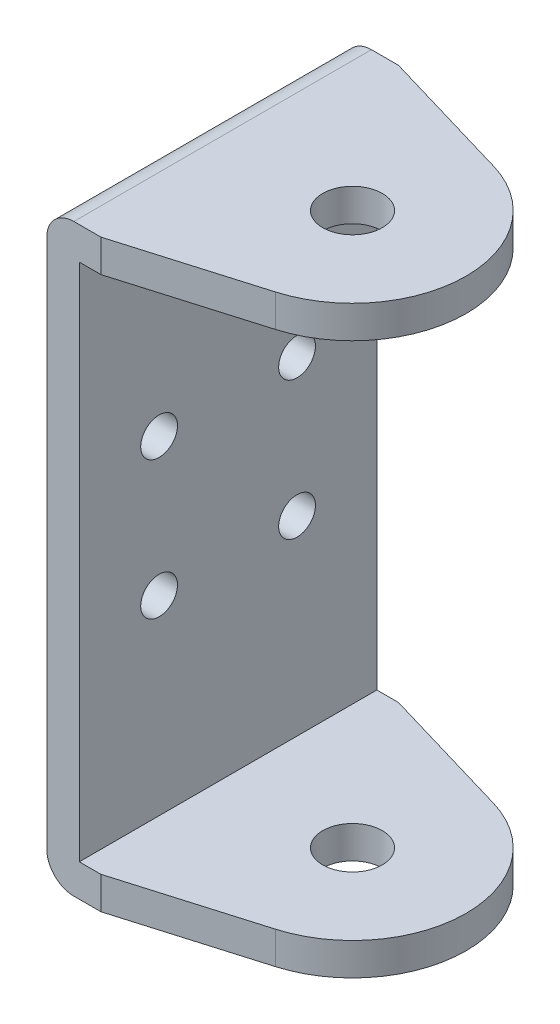
SolidWorks part; units mm, degrees
ref_plane "前基準面" through (0, 0, 0) normal (0, 0, 1) x (1, 0, 0)
ref_plane "上基準面" through (0, 0, 0) normal (0, 1, 0) x (1, 0, 0)
ref_plane "右基準面" through (0, 0, 0) normal (1, 0, 0) x (0, 0, -1)
sketch "草圖1" plane through (0, 0, 0) normal (0, 0, 1) x (1, 0, 0)
  line L0 (0, -54) -> (-45, -54)
  line L1 (0, 48) -> (-44, 48)
  line L2 (44, -48) -> (-44, -48) construction
  line L3 (0, -48) -> (-44, -48)
  line L4 (-44, 48) -> (-44, -48)
  line L5 (0, 0) -> (-44, -48) construction
  line L6 (0, 0) -> (-44, 48) construction
  line L7 (-50, 49) -> (-50, -49)
  line L8 (0, 54) -> (-45, 54)
  line L9 (50, -54) -> (-50, -54) construction
  line L10 (0, 65.9432) -> (0, -89.7922) construction
  line L11 (0, 54) -> (0, 48)
  line L12 (0, -48) -> (0, -54)
  line L13 (50, 54) -> (-50, 54) construction
  line L14 (44, 48) -> (-44, 48) construction
  line L15 (50, 54) -> (50, -54) construction
  line L16 (44, 48) -> (44, -48) construction
  line L17 (-50, 54) -> (-50, -54) construction
  line L18 (-44, 48) -> (-44, -48) construction
  line L19 (0, 0) -> (-107.849, 0) construction
  arc A0 (-45, -54) -> (-50, -49) centre (-45, -49) cw
  arc A2 (-50, 49) -> (-45, 54) centre (-45, 49) cw
  point P0 (0, 0)
  dimension "D5" = 5
  dimension "D6" = 5
  dimension "D1" = 6
  dimension "D2" = 108
  dimension "D3" = 50
  dimension "D4" = 96
extrude "填料-伸長1" add sketch "草圖1" along normal mid plane 55
hole_wizard "M10 螺紋孔1" positions "草圖4" profile "草圖3" tap size "M10" standard "ISO" end condition through all
sketch "草圖4" plane through (0, 54, 0) normal (0, 1, 0) x (1, 0, 0)
  line L0 (0, 0) -> (-21, 0) construction
  point P4 (-21, 0)
  dimension "D1" = 21
sketch "草圖3" plane through (-21, 54, 0) normal (1, 0, 0) x (0, 0, 1)
  line L0 (0, 0) -> (0, 108)
  line L1 (0, 108) -> (4.25, 108)
  line L2 (4.25, 108) -> (4.25, 0)
  line L5 (4.25, 0) -> (0, 0)
  line L11 (0, -6.35) -> (0, 107.95) construction
  dimension "貫穿螺孔鑽直徑" = 8.5
  dimension "貫穿螺孔鑽深度" = 108
cosmetic thread "鑽孔螺紋1" parameters "D2"=10
sketch "草圖6" plane through (-50, 0, 0) normal (-1, 0, 0) x (0, 0, 1)
  line L1 (12.75, 12.75) -> (12.75, -12.75) construction
  line L2 (12.75, 0) -> (0, 0) construction
  line L3 (0, 0) -> (-12.75, 0) construction
  line L4 (-12.75, -12.75) -> (-12.75, 12.75) construction
  circle A0 centre (12.75, 12.75) radius 3.4
  circle A1 centre (-12.75, 12.75) radius 3.4
  circle A2 centre (-12.75, -12.75) radius 3.4
  circle A3 centre (12.75, -12.75) radius 3.4
  dimension "D3" = 6.8
  dimension "D4" = 6.8
  dimension "D1" = 25.5
  dimension "D2" = 25.5
extrude "除料-伸長1" cut sketch "草圖6" against normal blind 10
cosmetic thread "裝飾螺紋線2" parameters "D2"=7
cosmetic thread "裝飾螺紋線3" parameters "D2"=7
cosmetic thread "裝飾螺紋線4" parameters "D2"=7
cosmetic thread "裝飾螺紋線5" parameters "D2"=7
sketch "草圖7" plane through (0, 54, 0) normal (0, 1, 0) x (1, 0, 0)
  circle A0 centre (-21, 0) radius 4.25 construction
  circle A1 centre (-21, 0) radius 4.25
  point P4 (-21, 0)
sketch "草圖8" plane through (0, -54, 0) normal (0, -1, 0) x (1, 0, 0)
  circle A0 centre (-21, 0) radius 4.25 construction
  circle A1 centre (-21, 0) radius 4.25
sketch "草圖9" plane through (0, 54, 0) normal (0, 1, 0) x (1, 0, 0)
  line L0 (-21, 0) -> (0, 0) construction
  circle A0 centre (-21, 0) radius 5
  dimension "D2" = 10
  dimension "D1" = 21
extrude "除料-伸長2" cut sketch "草圖9" against normal blind 136
sketch "草圖10" plane through (0, 54, 0) normal (0, 1, 0) x (1, 0, 0)
  line L3 (-40, 27.5) -> (-15.0579, 20.1418)
  line L4 (0, 27.5) -> (-45, 27.5) construction
  line L5 (-21, 0) -> (0, 0) construction
  line L6 (-40, -27.5) -> (-15.0579, -20.1418)
  line L7 (-50, -27.5) -> (-50, 27.5) construction
  arc A0 (-15.0579, -20.1418) -> (-15.0579, 20.1418) centre (-21, 0) ccw
  dimension "D1" = 10
extrude "除料-伸長3" cut sketch "草圖10" against normal through all and the other way through all flip side to cut
sketch "草圖13" plane through (-50, 0, 0) normal (-1, 0, 0) x (0, 0, 1)
  line L0 (0, -13.9476) -> (0, 45.385) construction
  line L1 (10.4791, 0) -> (-21.5487, 0) construction
  circle A0 centre (0, 42) radius 1.5
  circle A1 centre (0, -42) radius 1.5
  dimension "D1" = 3
  dimension "D2" = 84
  dimension "D3" = 42
extrude "除料-伸長4" [suppressed] cut sketch "草圖13" against normal up to next
cosmetic thread "裝飾螺紋線7" [suppressed] parameters "D2"=4
cosmetic thread "裝飾螺紋線8" [suppressed] parameters "D2"=4
sketch "草圖14" plane through (0, 54, 0) normal (0, 1, 0) x (1, 0, 0)
  circle A0 centre (-21, 0) radius 5.5
  dimension "D1" = 11
extrude "除料-伸長5" cut sketch "草圖14" against normal up to surface (108 mm away) up to face at (-26, -54, 0)
